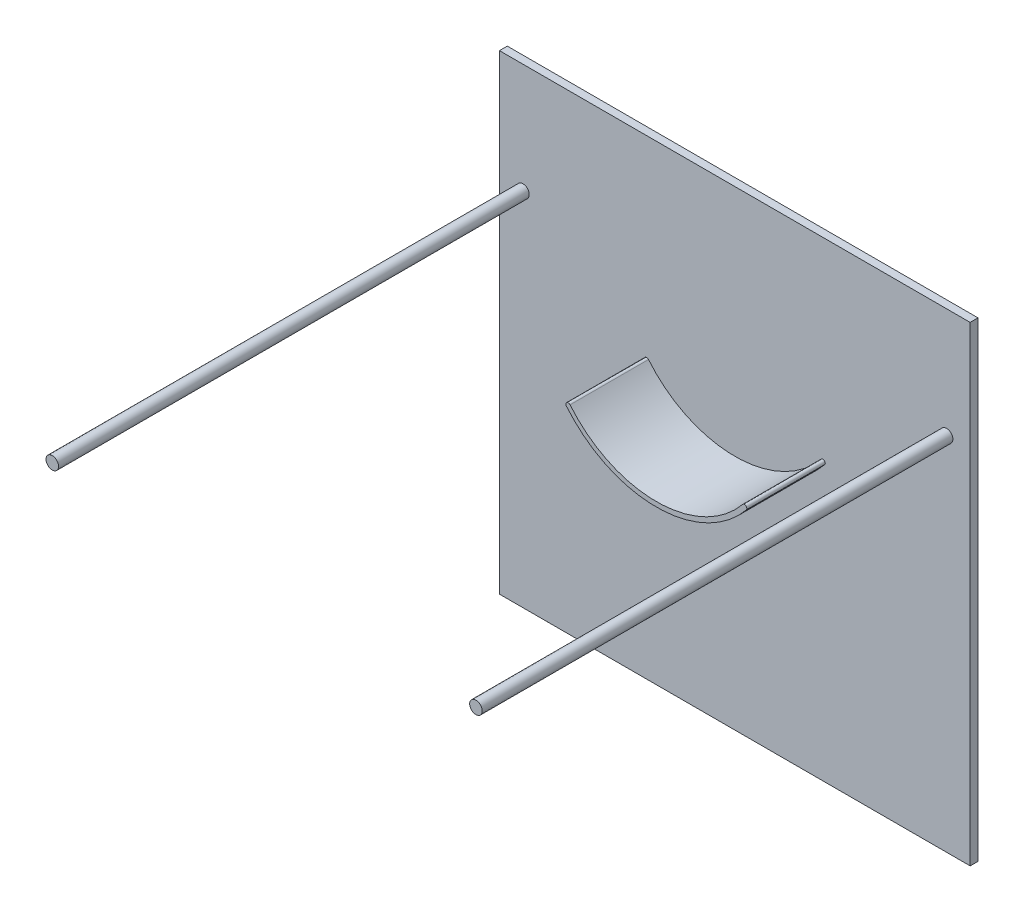
SolidWorks part; units mm, degrees
ref_plane "Plan de face" through (0, 0, 0) normal (0, 0, 1) x (1, 0, 0)
ref_plane "Plan de dessus" through (0, 0, 0) normal (0, 1, 0) x (1, 0, 0)
ref_plane "Plan de droite" through (0, 0, 0) normal (1, 0, 0) x (0, 0, -1)
sketch "Esquisse1" plane through (0, 0, 0) normal (0, 0, 1) x (1, 0, 0)
  line L1 (0, 0) -> (300, 0)
  line L2 (0, 0) -> (0, -300)
  line L3 (0, -300) -> (300, -300)
  line L4 (300, 0) -> (300, -300)
  dimension "D1" = 300
  dimension "D2" = 300
extrude "Boss.-Extru.1" add sketch "Esquisse1" along normal blind 5
sketch "Esquisse2" plane through (0, 0, 5) normal (0, 0, 1) x (1, 0, 0)
  line L0 (0, -70) -> (300, -70) construction
  line L1 (0, 0) -> (0, -300) construction
  line L2 (300, -300) -> (300, 0) construction
  line L3 (150, 0) -> (150, -137.0891) construction
  line L4 (300, 0) -> (0, 0) construction
  circle A0 centre (15, -70) radius 4
  circle A1 centre (285, -70) radius 4
  dimension "D2" = 8
  dimension "D1" = 70
  dimension "D3" = 15
extrude "Boss.-Extru.2" add sketch "Esquisse2" along normal blind 300
sketch "Esquisse3" plane through (0, 0, 5) normal (0, 0, 1) x (1, 0, 0)
  line L0 (150, 0) -> (150, -227.6466) construction
  line L1 (300, 0) -> (0, 0) construction
  circle A0 centre (150, -70) radius 10
  dimension "D1" = 20
  dimension "D2" = 70
sketch "Esquisse4" plane through (0, 0, 5) normal (0, 0, 1) x (1, 0, 0)
  line L0 (150, -70) -> (150, -181.1381) construction
  arc A0 (103.5967, -111.1186) -> (196.4033, -111.1186) centre (150, -70) ccw
  arc A1 (99.8545, -114.4346) -> (200.1455, -114.4346) centre (150, -70) ccw
  arc A2 (103.5967, -111.1186) -> (99.8545, -114.4346) centre (101.7256, -112.7766) ccw
  arc A3 (196.4033, -111.1186) -> (200.1455, -114.4346) centre (198.2744, -112.7766) cw
  dimension "D4" = 62
  dimension "D1" = 84
  dimension "D2" = 84
  dimension "D3" = 5
extrude "Boss.-Extru.3" [suppressed] add sketch "Esquisse4" along normal blind 200
sketch "Esquisse5" plane through (0, 0, 5) normal (0, 0, 1) x (1, 0, 0)
  line L0 (150, 0) -> (150, -300) construction
  arc A1 (95, -122.9915) -> (205, -122.9915) centre (150, -77.6237) ccw
  arc A2 (92.6857, -124.9005) -> (207.3143, -124.9005) centre (150, -77.6237) ccw
  arc A3 (95, -122.9915) -> (92.6857, -124.9005) centre (93.8429, -123.946) ccw
  arc A4 (205, -122.9915) -> (207.3143, -124.9005) centre (206.1571, -123.946) cw
  dimension "D1" = 55
  dimension "D2" = 55
  dimension "D3" = 3
extrude "Boss.-Extru.4" add sketch "Esquisse5" along normal blind 50
